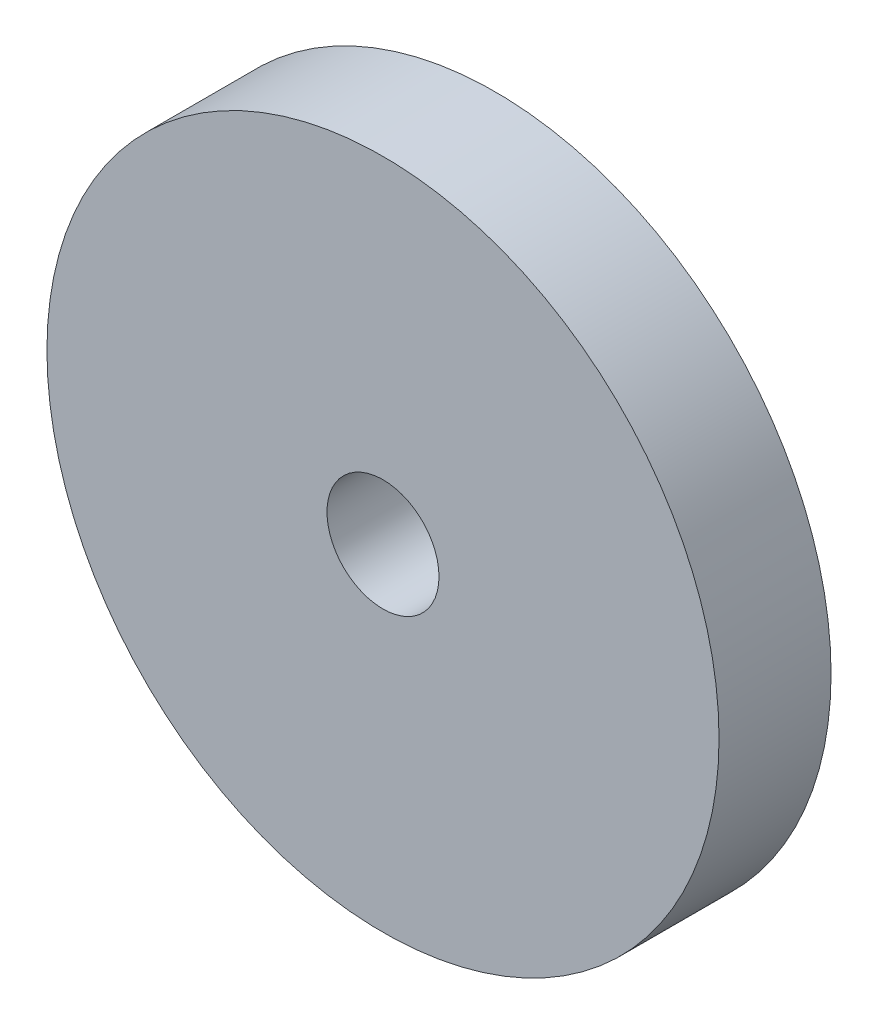
SolidWorks part; units mm, degrees
ref_plane "Front Plane" through (0, 0, 0) normal (0, 0, 1) x (1, 0, 0)
ref_plane "Top Plane" through (0, 0, 0) normal (0, 1, 0) x (1, 0, 0)
ref_plane "Right Plane" through (0, 0, 0) normal (1, 0, 0) x (0, 0, -1)
sketch "Sketch1" plane through (0, 0, 0) normal (0, 0, 1) x (1, 0, 0)
  circle A0 centre (0, 0) radius 60
  dimension "D1" = 120
extrude "Boss-Extrude2" add sketch "Sketch1" along normal blind 20
sketch "Sketch2" plane through (0, 0, 20) normal (0, 0, 1) x (1, 0, 0)
  circle A0 centre (0, 0) radius 10
  circle A1 centre (0, 0) radius 60 construction
  dimension "D1" = 20
extrude "Cut-Extrude1" cut sketch "Sketch2" against normal through all
